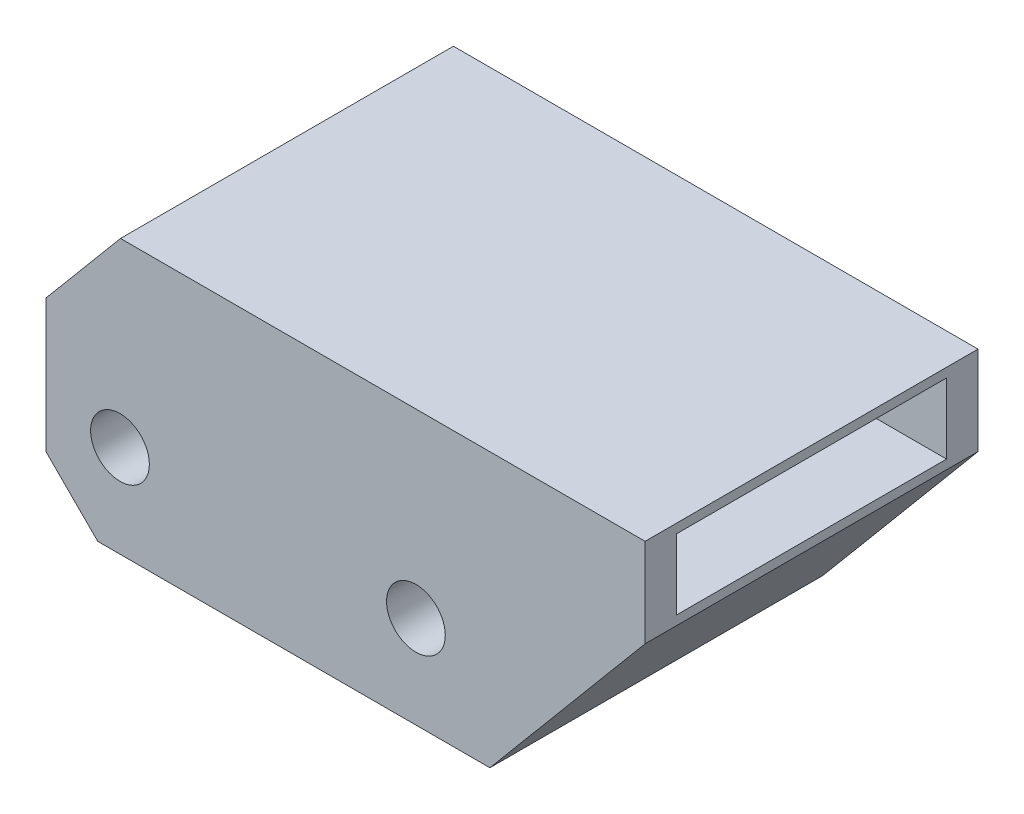
SolidWorks part; units mm, degrees
material "ABS"
ref_plane "Plano frontal" through (0, 0, 0) normal (0, 0, 1) x (1, 0, 0)
ref_plane "Plano superior" through (0, 0, 0) normal (0, 1, 0) x (1, 0, 0)
ref_plane "Plano direito" through (0, 0, 0) normal (1, 0, 0) x (0, 0, -1)
sketch "Esboço1" plane through (0, 0, 0) normal (0, 0, 1) x (1, 0, 0)
  line L0 (-30, 0) -> (-20, 0) construction
  line L1 (30, -12.5) -> (-30, -12.5)
  line L4 (-30, -12.5) -> (-30, 12.5)
  line L5 (30, -12.5) -> (-30, 12.5) construction
  line L6 (30, 12.5) -> (-30, -12.5) construction
  line L7 (-20, 0) -> (20, 0) construction
  line L8 (20, 0) -> (30, 0) construction
  line L10 (30.9775, 24.5) -> (-19.9308, 24.5)
  line L11 (-19.9308, 24.5) -> (-30, 12.5)
  line L12 (-30, 12.5) -> (30, 12.5) construction
  line L13 (30.9775, 24.5) -> (50.9775, 24.5)
  line L14 (50.9775, 24.5) -> (50.9775, 12.5)
  line L15 (50.9775, 12.5) -> (30, -12.5)
  line L16 (30, 12.5) -> (30, -12.5) construction
  line L17 (30, 12.5) -> (50.9775, 12.5) construction
  circle A0 centre (-20, 0) radius 3.97
  circle A1 centre (20, 0) radius 3.97
  point P0 (0, 0)
  dimension "D4" = 7.94
  dimension "D1" = 60
  dimension "D2" = 25
  dimension "D3" = 40
  dimension "D5" = 12
  dimension "D6" = 50
  dimension "D7" = 20
  dimension "D8" = 40
extrude "Ressalto-extrusão1" add sketch "Esboço1" along normal mid plane 45
sketch "Esboço2" plane through (50.9775, 0, 0) normal (1, 0, 0) x (0, 0, -1)
  line L0 (-22.5, 18.5) -> (22.5, 18.5) construction
  line L1 (-22.5, 12.5) -> (-22.5, 24.5) construction
  line L2 (22.5, 12.5) -> (22.5, 24.5) construction
  line L3 (0, 24.5) -> (0, 12.5) construction
  line L4 (-22.5, 24.5) -> (22.5, 24.5) construction
  line L5 (-22.5, 12.5) -> (22.5, 12.5) construction
  line L7 (18.25, 13.75) -> (-18.25, 13.75)
  line L8 (18.25, 13.75) -> (18.25, 23.25)
  line L9 (18.25, 23.25) -> (-18.25, 23.25)
  line L10 (-18.25, 13.75) -> (-18.25, 23.25)
  line L11 (18.25, 13.75) -> (-18.25, 23.25) construction
  line L12 (18.25, 23.25) -> (-18.25, 13.75) construction
  point P12 (0, 18.5)
  dimension "D1" = 9.5
  dimension "D2" = 36.5
extrude "Corte-extrusão1" cut sketch "Esboço2" against normal blind 25
chamfer "Chanfro1" distance 7 angle 45 1 edges at (-30, -12.5, 0)
